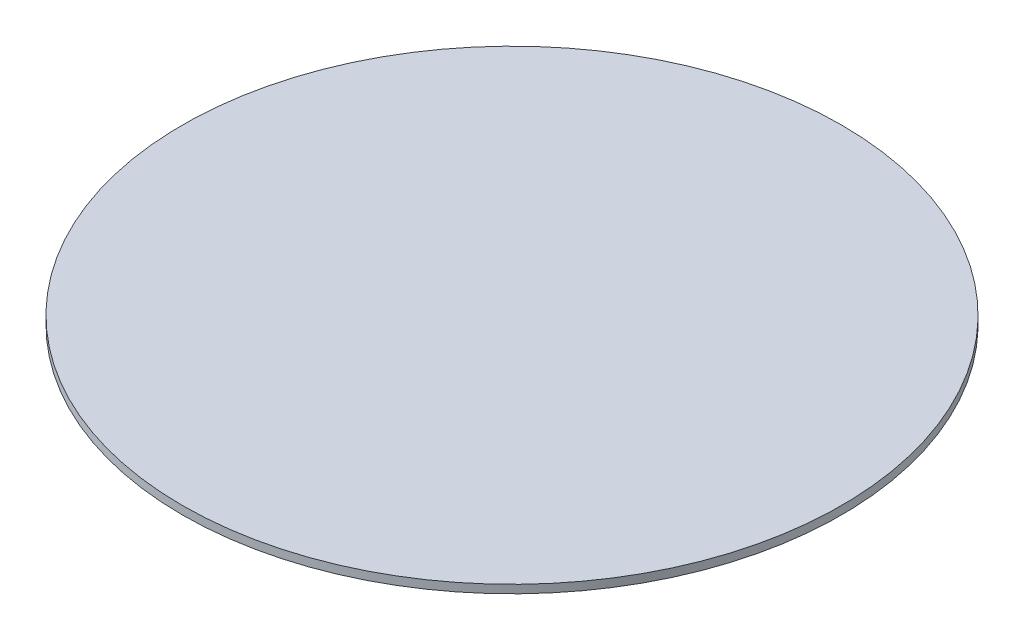
SolidWorks part; units mm, degrees
material "PTFE (general)"
ref_plane "Front Plane" through (0, 0, 0) normal (0, 0, 1) x (1, 0, 0)
ref_plane "Top Plane" through (0, 0, 0) normal (0, 1, 0) x (1, 0, 0)
ref_plane "Right Plane" through (0, 0, 0) normal (1, 0, 0) x (0, 0, -1)
sketch "Sketch1" plane through (0, 0, 0) normal (0, 1, 0) x (1, 0, 0)
  circle A0 centre (0, 0) radius 15.875
  dimension "D1" = 31.75
extrude "Boss-Extrude1" add sketch "Sketch1" along normal blind 0.3969
